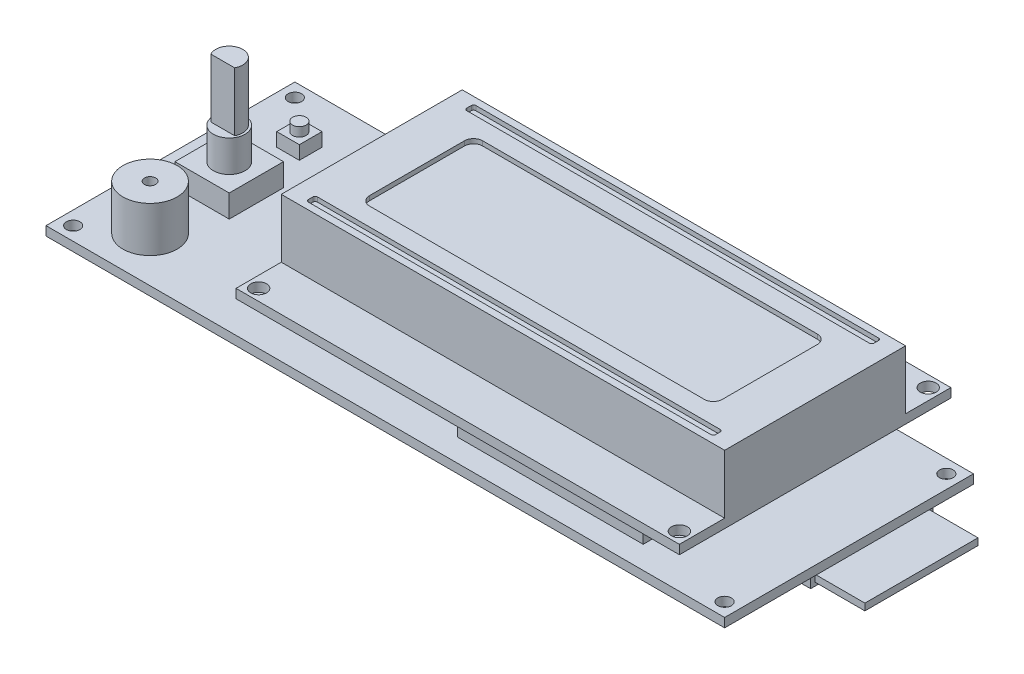
SolidWorks part; units mm, degrees
ref_plane "Front Plane" through (0, 0, 0) normal (0, 0, 1) x (1, 0, 0)
ref_plane "Top Plane" through (0, 0, 0) normal (0, 1, 0) x (1, 0, 0)
ref_plane "Right Plane" through (0, 0, 0) normal (1, 0, 0) x (0, 0, -1)
sketch "Sketch1" plane through (0, 0, 0) normal (0, 1, 0) x (1, 0, 0)
  line L0 (75, 55) -> (75, 0) construction
  line L1 (0, 0) -> (150, 0)
  line L2 (0, 0) -> (0, 55)
  line L3 (0, 55) -> (150, 55)
  line L4 (150, 0) -> (150, 55)
  line L5 (0, 27.5) -> (150, 27.5) construction
  circle A0 centre (3, 52) radius 1.5
  circle A1 centre (147, 52) radius 1.5
  circle A2 centre (147, 3) radius 1.5
  circle A3 centre (3, 3) radius 1.5
  dimension "D3" = 3
  dimension "D1" = 55
  dimension "D2" = 150
  dimension "D4" = 3
  dimension "D5" = 3
extrude "Boss-Extrude1" add sketch "Sketch1" along normal blind 2
sketch "Sketch2" plane through (0, 2, 0) normal (0, 1, 0) x (1, 0, 0)
  line L0 (0, 0) -> (150, 0) construction
  line L1 (0, 0) -> (0, 55) construction
  circle A0 centre (13, 10) radius 6
  dimension "D1" = 12
  dimension "D2" = 10
  dimension "D3" = 13
extrude "Boss-Extrude2" add sketch "Sketch2" along normal blind 10
sketch "Sketch3" plane through (0, 2, 0) normal (0, 1, 0) x (1, 0, 0)
  line L0 (0, 27.5) -> (150, 27.5) construction
  line L1 (7, 33.5) -> (19, 33.5)
  line L2 (7, 33.5) -> (7, 21.5)
  line L3 (7, 21.5) -> (19, 21.5)
  line L4 (19, 33.5) -> (19, 21.5)
  line L5 (13, 0) -> (13, 55) construction
  line L6 (0, 0) -> (150, 0) construction
  line L7 (0, 55) -> (150, 55) construction
  line L8 (7, 27.5) -> (19, 27.5) construction
  circle A1 centre (13, 10) radius 6 construction
  point P4 (7, 27.5)
  point P16 (13, 27.5)
  point P19 (13, 16)
  dimension "D1" = 12
  dimension "D2" = 12
extrude "Boss-Extrude3" add sketch "Sketch3" along normal blind 25
sketch "Sketch4" plane through (0, 2, 0) normal (0, 1, 0) x (1, 0, 0)
  line L0 (13, 45.5) -> (13, 40.5) construction
  line L1 (10.5, 45.5) -> (15.5, 45.5)
  line L2 (10.5, 45.5) -> (10.5, 40.5)
  line L3 (10.5, 40.5) -> (15.5, 40.5)
  line L4 (15.5, 45.5) -> (15.5, 40.5)
  line L5 (10.5, 43) -> (15.5, 43) construction
  line L7 (13, 0) -> (13, 55) construction
  line L8 (7, 33.5) -> (19, 33.5) construction
  line L9 (150, 0) -> (150, 55) construction
  line L10 (127, 8) -> (86, 8)
  line L11 (127, 8) -> (127, 5)
  line L12 (127, 5) -> (86, 5)
  line L13 (86, 8) -> (86, 5)
  line L14 (0, 0) -> (150, 0) construction
  point P8 (13, 43)
  dimension "D1" = 5
  dimension "D2" = 5
  dimension "D3" = 7
  dimension "D4" = 23
  dimension "D5" = 41
  dimension "D6" = 3
  dimension "D7" = 5
extrude "Boss-Extrude4" add sketch "Sketch4" along normal blind 5
sketch "Sketch5" plane through (0, 7, 0) normal (0, 1, 0) x (1, 0, 0)
  line L0 (86, 5) -> (127, 5) construction
  line L1 (86, 8) -> (127, 8)
  line L2 (86, 8) -> (86, 5)
  line L3 (86, 5) -> (127, 5)
  line L4 (127, 8) -> (127, 5)
  line L5 (86, 5) -> (127, 5) construction
  line L6 (10.5, 43) -> (15.5, 43) construction
  line L7 (10.5, 45.5) -> (10.5, 40.5) construction
  line L8 (15.5, 40.5) -> (15.5, 45.5) construction
  line L10 (10.5, 45.5) -> (15.5, 45.5)
  line L11 (10.5, 45.5) -> (10.5, 40.5)
  line L12 (10.5, 40.5) -> (15.5, 40.5)
  line L13 (15.5, 45.5) -> (15.5, 40.5)
  circle A0 centre (13, 43) radius 1.5
  point P15 (13, 43)
  dimension "D1" = 3
extrude "Cut-Extrude1" cut sketch "Sketch5" against normal blind 2
sketch "Sketch6" plane through (0, 27, 0) normal (0, 1, 0) x (1, 0, 0)
  line L0 (10.3706, 26.0556) -> (15.6294, 26.0556)
  line L1 (7, 33.5) -> (19, 33.5)
  line L2 (7, 33.5) -> (7, 21.5)
  line L3 (7, 21.5) -> (19, 21.5)
  line L4 (19, 33.5) -> (19, 21.5)
  arc A0 (15.6294, 26.0556) -> (10.3706, 26.0556) centre (13, 27.5) ccw
  dimension "D1" = 6
extrude "Cut-Extrude2" cut sketch "Sketch6" against normal blind 13
sketch "Sketch7" plane through (0, 14, 0) normal (0, 1, 0) x (1, 0, 0)
  line L1 (7, 33.5) -> (19, 33.5)
  line L2 (7, 33.5) -> (7, 21.5)
  line L3 (7, 21.5) -> (19, 21.5)
  line L4 (19, 33.5) -> (19, 21.5)
  circle A0 centre (13, 27.5) radius 3.5
  line M4 (7, 33.5) -> (7, 21.5)
  line M5 (7, 21.5) -> (19, 21.5)
  line M6 (19, 21.5) -> (19, 33.5)
  line M7 (19, 33.5) -> (7, 33.5)
  dimension "D1" = 7
extrude "Cut-Extrude3" cut sketch "Sketch7" against normal blind 7 contours A0 M7 M4 M5 M6
sketch "Sketch8" plane through (0, 12, 0) normal (0, 1, 0) x (1, 0, 0)
  circle A0 centre (13, 10) radius 1.25
  point P0 (13, 10)
  dimension "D1" = 2.5
extrude "Cut-Extrude4" cut sketch "Sketch8" against normal blind 5
sketch "Sketch9" plane through (0, 0, 0) normal (0, -1, 0) x (1, 0, 0)
  line L0 (0, -55) -> (150, -55) construction
  line L1 (149, -20) -> (131, -20)
  line L2 (149, -20) -> (149, -47)
  line L3 (149, -47) -> (124, -47)
  line L4 (124, -22) -> (124, -47)
  line L5 (150, 0) -> (150, -55) construction
  line L6 (124, -22) -> (129, -22)
  line L7 (129, -22) -> (131, -20)
  dimension "D1" = 8
  dimension "D2" = 27
  dimension "D3" = 1
  dimension "D4" = 25
  dimension "D5" = 2
  dimension "D6" = 5
  dimension "D7" = 45
extrude "Boss-Extrude5" add sketch "Sketch9" along normal blind 3
sketch "Sketch10" plane through (149, 0, 0) normal (1, 0, 0) x (0, 0, -1)
  line L0 (20, -1.5) -> (47, -1.5) construction
  line L1 (20, -3) -> (20, 0) construction
  line L2 (47, -3) -> (47, 0) construction
  line L3 (33.5, -3) -> (33.5, 0) construction
  line L4 (47, -3) -> (20, -3) construction
  line L5 (0, 0) -> (55, 0) construction
  line L6 (33.5, -2.25) -> (33.5, -0.75) construction
  line L7 (21, -2.25) -> (46, -2.25)
  line L8 (21, -2.25) -> (21, -0.75)
  line L9 (21, -0.75) -> (46, -0.75)
  line L10 (46, -2.25) -> (46, -0.75)
  line L11 (21, -1.5) -> (46, -1.5) construction
  point P20 (33.5, -1.5)
  point P21 (33.5, -1.5)
  dimension "D1" = 1.5
  dimension "D2" = 25
extrude "Cut-Extrude5" cut sketch "Sketch10" against normal blind 18
sketch "Sketch11" plane through (0, 5, 0) normal (0, 1, 0) x (1, 0, 0)
  line L0 (0, 0) -> (150, 0) construction
  line L1 (136, 64) -> (38, 64)
  line L2 (136, 64) -> (136, 4)
  line L3 (136, 4) -> (38, 4)
  line L4 (38, 64) -> (38, 4)
  line L5 (150, 0) -> (150, 55) construction
  line L6 (87, 64) -> (87, 4) construction
  line L7 (38, 34) -> (136, 34) construction
  circle A0 centre (40.5, 61.5) radius 1.75
  circle A1 centre (133.5, 61.5) radius 1.75
  circle A2 centre (133.5, 6.5) radius 1.75
  circle A3 centre (40.5, 6.5) radius 1.75
  point P12 (87, 34)
  dimension "D5" = 3.5
  dimension "D1" = 98
  dimension "D2" = 60
  dimension "D3" = 4
  dimension "D4" = 14
  dimension "D6" = 2.5
  dimension "D7" = 2.5
extrude "Boss-Extrude6" add sketch "Sketch11" along normal blind 2
sketch "Sketch12" plane through (0, 7, 0) normal (0, 1, 0) x (1, 0, 0)
  line L0 (38, 34) -> (136, 34) construction
  line L1 (38, 54) -> (136, 54)
  line L2 (38, 54) -> (38, 14)
  line L3 (38, 14) -> (136, 14)
  line L4 (136, 54) -> (136, 14)
  dimension "D1" = 40
extrude "Boss-Extrude7" add sketch "Sketch12" along normal blind 13
sketch "Sketch13" plane through (0, 20, 0) normal (0, 1, 0) x (1, 0, 0)
  line L0 (87, 54) -> (87, 14) construction
  line L1 (136, 54) -> (38, 54) construction
  line L2 (38, 14) -> (136, 14) construction
  line L3 (38, 34) -> (136, 34) construction
  line L4 (38, 54) -> (38, 14) construction
  line L5 (136, 14) -> (136, 54) construction
  line L6 (87, 46.5) -> (87, 21.5) construction
  line L7 (50, 46.5) -> (124, 46.5)
  line L8 (48, 44.5) -> (48, 23.5)
  line L9 (50, 21.5) -> (124, 21.5)
  line L10 (126, 44.5) -> (126, 23.5)
  line L11 (87, 52.5) -> (87, 50.5) construction
  line L12 (42.5, 52.5) -> (131.5, 52.5)
  line L13 (42, 52) -> (42, 51)
  line L14 (42.5, 50.5) -> (131.5, 50.5)
  line L15 (132, 52) -> (132, 51)
  line L16 (136, 54) -> (38, 54) construction
  line L17 (42, 52.5) -> (42, 50.5)
  line L18 (132, 52.5) -> (132, 50.5)
  line L19 (87, 15.5) -> (87, 17.5) construction
  line L20 (132, 16) -> (132, 17)
  line L21 (42, 16) -> (42, 17)
  line L22 (132, 15.5) -> (132, 17.5)
  line L23 (42.5, 17.5) -> (131.5, 17.5)
  line L24 (42, 15.5) -> (42, 17.5)
  line L25 (42.5, 15.5) -> (131.5, 15.5)
  arc A0 (131.5, 50.5) -> (132, 51) centre (131.5, 51) ccw
  arc A1 (131.5, 52.5) -> (132, 52) centre (131.5, 52) cw
  arc A2 (42, 51) -> (42.5, 50.5) centre (42.5, 51) ccw
  arc A3 (42.5, 52.5) -> (42, 52) centre (42.5, 52) ccw
  arc A4 (131.5, 15.5) -> (132, 16) centre (131.5, 16) ccw
  arc A5 (131.5, 17.5) -> (132, 17) centre (131.5, 17) cw
  arc A6 (42.5, 15.5) -> (42, 16) centre (42.5, 16) cw
  arc A7 (42.5, 17.5) -> (42, 17) centre (42.5, 17) ccw
  arc A8 (124, 46.5) -> (126, 44.5) centre (124, 44.5) cw
  arc A9 (48, 23.5) -> (50, 21.5) centre (50, 23.5) ccw
  arc A10 (50, 46.5) -> (48, 44.5) centre (50, 44.5) ccw
  arc A11 (124, 21.5) -> (126, 23.5) centre (124, 23.5) ccw
  point P18 (87, 34)
  point P19 (87, 34)
  point P62 (48, 21.5)
  point P65 (48, 46.5)
  dimension "D6" = 0.5
  dimension "D7" = 0.5
  dimension "D8" = 2
  dimension "D1" = 25
  dimension "D2" = 10
  dimension "D3" = 4
  dimension "D4" = 1.5
  dimension "D5" = 2
extrude "Cut-Extrude6" cut sketch "Sketch13" against normal blind 1 contours L15 L12 L13 L14 | L10 L7 L8 L9 | L21 L25 L20 L23
sketch "Sketch14" plane through (131, 0, 0) normal (1, 0, 0) x (0, 0, -1)
  line L1 (21, -0.75) -> (46, -0.75)
  line L2 (21, -0.75) -> (21, -2.25)
  line L3 (21, -2.25) -> (46, -2.25)
  line L4 (46, -0.75) -> (46, -2.25)
extrude "Boss-Extrude8" add sketch "Sketch14" along normal offset from surface (29 mm away) 11 up to face at (149, -1.5, -33.5) offset beyond the face yes
